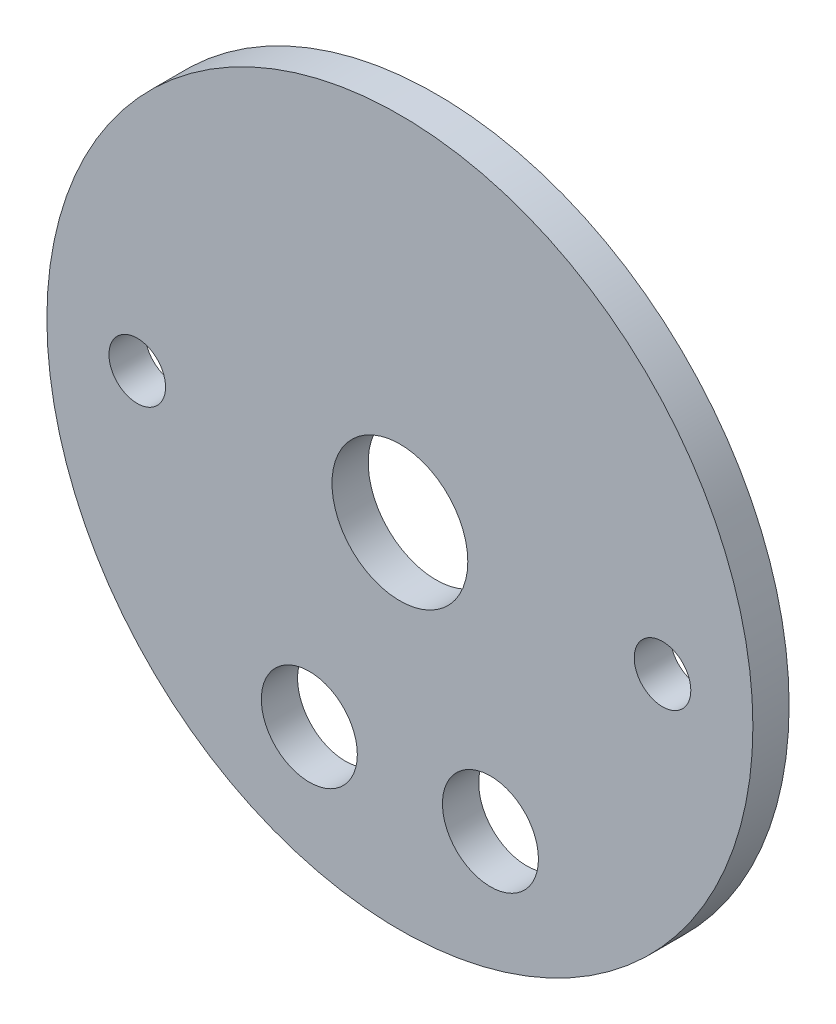
SolidWorks part; units mm, degrees
ref_plane "Front Plane" through (0, 0, 0) normal (0, 0, 1) x (1, 0, 0)
ref_plane "Top Plane" through (0, 0, 0) normal (0, 1, 0) x (1, 0, 0)
ref_plane "Right Plane" through (0, 0, 0) normal (1, 0, 0) x (0, 0, -1)
sketch "Sketch1" plane through (0, 0, 0) normal (0, 0, 1) x (1, 0, 0)
  circle A0 centre (0, 0) radius 49.5046
  dimension "D1" = 99.0092
extrude "Boss-Extrude1" add sketch "Sketch1" along normal blind 5.08
sketch "Sketch2" plane through (0, 0, 5.08) normal (0, 0, 1) x (1, 0, 0)
  circle A0 centre (0, 0) radius 47.625
  dimension "D1" = 95.25
extrude "Boss-Extrude2" add sketch "Sketch2" along normal blind 3.175
sketch "Sketch3" plane through (0, 0, 8.255) normal (0, 0, 1) x (1, 0, 0)
  circle A0 centre (-12.7, -31.1668) radius 6.731
  circle A1 centre (12.7, -31.1668) radius 6.731
  circle A2 centre (-12.7, -31.1668) radius 12.7 construction
  circle A3 centre (-12.7, -31.1668) radius 13.97 construction
  circle A4 centre (12.7, -31.1668) radius 12.7 construction
  circle A5 centre (12.7, -31.1668) radius 13.97 construction
  circle A6 centre (0, 0) radius 47.625 construction
  circle A7 centre (0, 0) radius 47.625 construction
  circle A8 centre (-36.83, 0) radius 3.9687
  circle A9 centre (36.83, 0) radius 3.9687
  circle A10 centre (0, 0) radius 9.525
  dimension "D1" = 27.94
  dimension "D2" = 25.4
  dimension "D3" = 13.462
  dimension "D4" = 7.9375
  dimension "D5" = 7.9375
  dimension "D8" = 19.05
  dimension "D6" = 73.66
  dimension "D7" = 36.83
extrude "Cut-Extrude1" cut sketch "Sketch3" against normal through all
sketch "Sketch4" plane through (0, 0, 8.255) normal (0, 0, 1) x (1, 0, 0)
  circle A0 centre (0, 0) radius 55.7081
extrude "Cut-Extrude2" cut sketch "Sketch4" against normal blind 3.175
